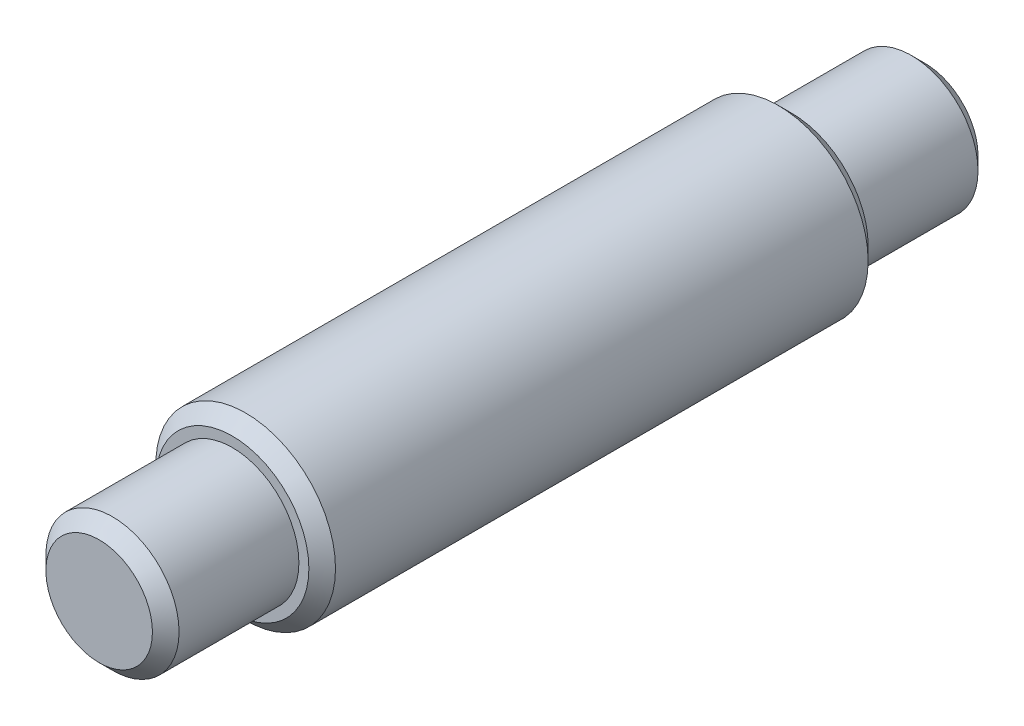
SolidWorks part; units mm, degrees
ref_plane "Front Plane" through (0, 0, 0) normal (0, 0, 1) x (1, 0, 0)
ref_plane "Top Plane" through (0, 0, 0) normal (0, 1, 0) x (1, 0, 0)
ref_plane "Right Plane" through (0, 0, 0) normal (1, 0, 0) x (0, 0, -1)
sketch "Sketch1" plane through (0, 0, 0) normal (0, 0, 1) x (1, 0, 0)
  circle A0 centre (0, 0) radius 0.25
  dimension "D1" = 0.5
extrude "Boss-Extrude1" add sketch "Sketch1" against normal mid plane 3.1
sketch "Sketch3" plane through (0, 0, 0) normal (0, 0, 1) x (1, 0, 0)
  circle A0 centre (0, 0) radius 0.3375
extrude "Boss-Extrude2" add sketch "Sketch3" along normal mid plane 2.1
chamfer "Chamfer1" distance 0.05 angle 45 4 edges at (0.3375, 0, -1.05) (0.25, 0, -1.55) (0.25, 0, 1.55) (0.3375, 0, 1.05)
